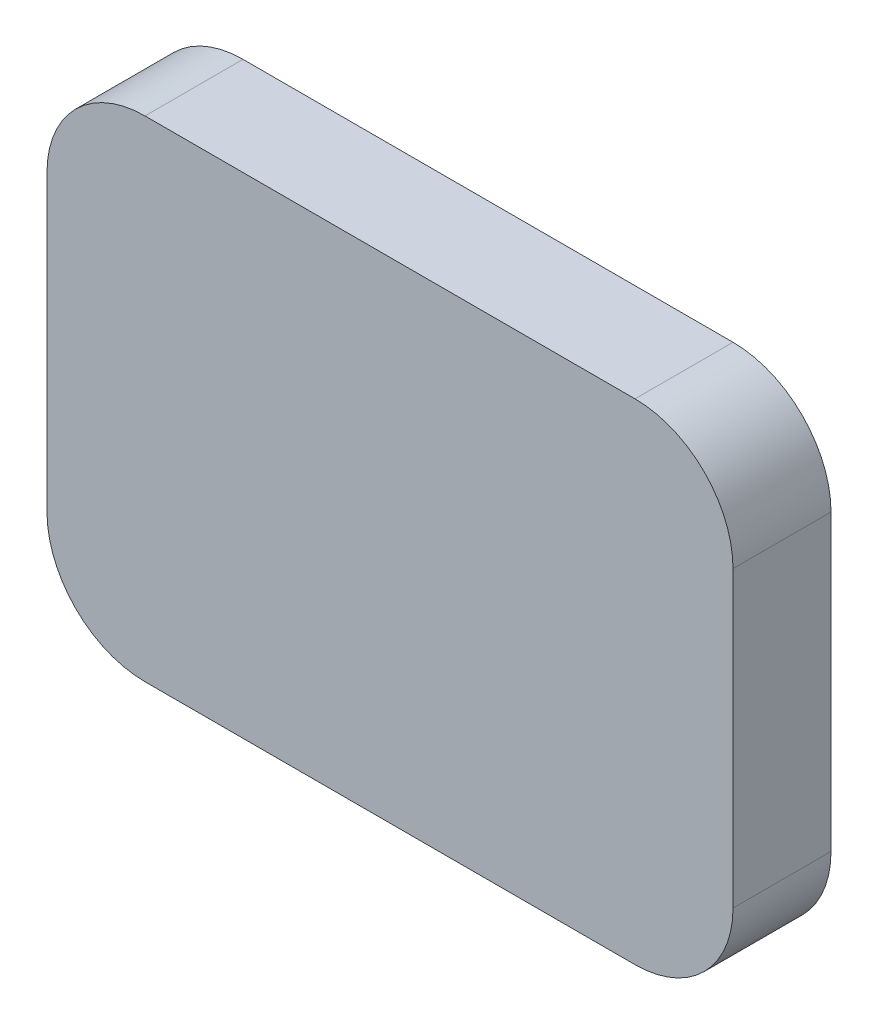
SolidWorks part; units mm, degrees
ref_plane "정면" through (0, 0, 0) normal (0, 0, 1) x (1, 0, 0)
ref_plane "윗면" through (0, 0, 0) normal (0, 1, 0) x (1, 0, 0)
ref_plane "우측면" through (0, 0, 0) normal (1, 0, 0) x (0, 0, -1)
sketch "스케치1" plane through (0, 0, 0) normal (0, 0, 1) x (1, 0, 0)
  line L1 (0, 0) -> (70, 0)
  line L2 (0, 0) -> (0, -50)
  line L3 (0, -50) -> (70, -50)
  line L4 (70, 0) -> (70, -50)
  dimension "D1" = 70
  dimension "D2" = 50
extrude "보스-돌출1" add sketch "스케치1" along normal blind 10
fillet "필렛1" radius 10 4 edges at (0, -50, 5) (0, 0, 5) (70, -50, 5) (70, 0, 5)
